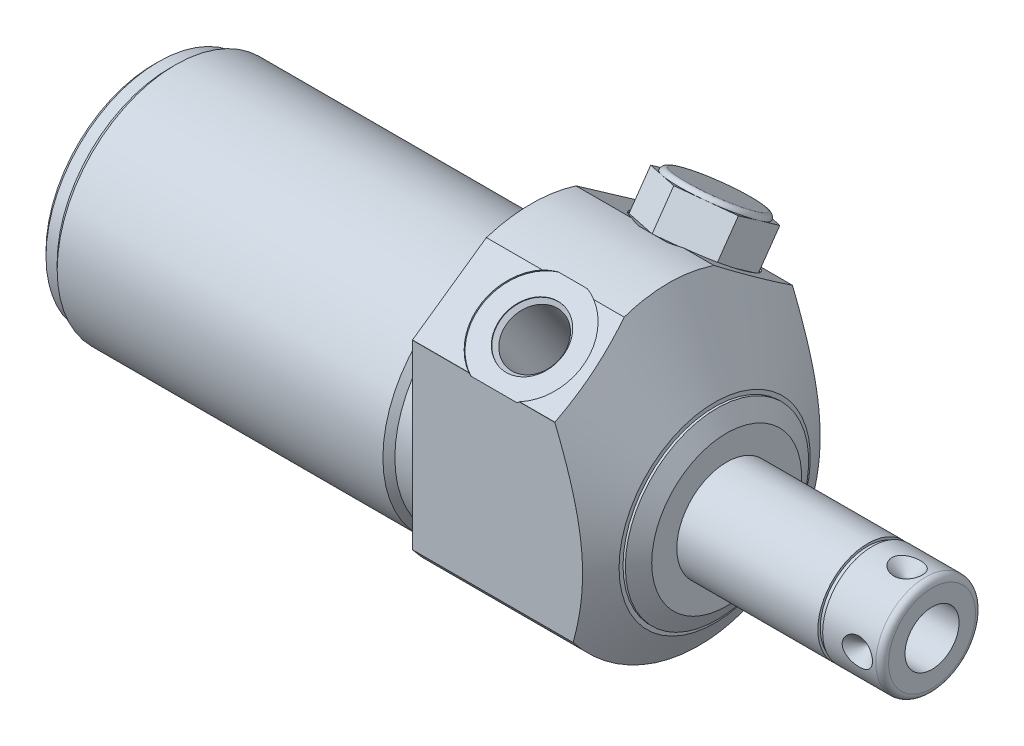
SolidWorks part; units mm, degrees
material "Alloy Steel"
ref_plane "Front Plane" through (0, 0, 0) normal (0, 0, 1) x (1, 0, 0)
ref_plane "Top Plane" through (0, 0, 0) normal (0, 1, 0) x (1, 0, 0)
ref_plane "Right Plane" through (0, 0, 0) normal (1, 0, 0) x (0, 0, -1)
sketch "Sketch1" plane through (0, 0, 0) normal (1, 0, 0) x (0, 0, -1)
  circle A0 centre (0, 0) radius 25.4
  dimension "D1" = 50.8
extrude "Extrude1" add sketch "Sketch1" along normal blind 31.1404 and the other way blind 60.1472
sketch "Sketch2" plane through (0, 0, 0) normal (1, 0, 0) x (0, 0, -1)
  line L0 (-14.6964, -4.191) -> (14.6964, -4.191) construction
  circle A0 centre (0, -4.191) radius 18.8595
  circle A1 centre (0, 0) radius 25.4 construction
  circle A2 centre (0, 0) radius 25.4
  dimension "D1" = 37.719
  dimension "D2" = 4.191
extrude "Cut-Extrude1" cut sketch "Sketch2" against normal up to next
sketch "Sketch4" plane through (31.1404, 0, 0) normal (-1, 0, 0) x (0, 0, 1)
  line L0 (18.923, -14.4553) -> (18.923, 14.4553)
  line L1 (18.9056, 14.4781) -> (7.1389, 22.7172)
  line L2 (-18.923, -14.4553) -> (-18.923, 14.4553)
  line L3 (-18.9056, 14.4781) -> (-7.1389, 22.7172)
  line L4 (0, -20.9029) -> (0, 19.86) construction
  circle A0 centre (0, 0) radius 25.4 construction
  circle A1 centre (0, 0) radius 25.4
  arc A2 (-18.923, -14.4553) -> (18.923, -14.4553) centre (0, 0) ccw
  arc A3 (7.1389, 22.7172) -> (-7.1389, 22.7172) centre (0, 0) ccw
  arc A4 (18.923, 14.4553) -> (18.9056, 14.4781) centre (0, 0) ccw
  arc A6 (-18.9056, 14.4781) -> (-18.923, 14.4553) centre (0, 0) ccw
  dimension "D4" = 23.8125
  dimension "D1" = 37.846
  dimension "D2" = 55
  dimension "D3" = 26.1366
extrude "Cut-Extrude3" cut sketch "Sketch4" along normal up to next
sketch "Sketch6" plane through (0, 0, 0) normal (0, 0, 1) x (1, 0, 0)
  line L0 (16.3822, 33.309) -> (29.2354, 11.0466)
  line L1 (1.9872, -4.191) -> (19.8625, -4.191) construction
  line L2 (-60.1472, -4.191) -> (0, -4.191) construction
  line L4 (31.1404, 7.747) -> (31.1404, 33.309)
  line L5 (31.1404, 33.309) -> (16.3822, 33.309)
  line L7 (29.2354, 11.0466) -> (29.2354, 10.414)
  line L8 (29.2354, 10.414) -> (29.6006, 10.414)
  line L9 (29.6006, 10.414) -> (31.1404, 7.747)
  line L11 (31.1404, -14.4553) -> (31.1404, 14.4553) construction
  dimension "D1" = 23.876
  dimension "D2" = 75
  dimension "D3" = 29.21
  dimension "D4" = 1.905
  dimension "D5" = 30
revolve "Cut-Revolve2" cut sketch "Sketch6" angle 360 about L1
ref_plane "Plane17" through (13.0048, 0, 0) normal (-1, 0, 0) x (0, 0, 1)
sketch "S2D0002" plane through (13.0048, 13.7124, 8.6091) normal (1, 0, 0) x (0, 0.4226, -0.9063)
  line L0 (3.0583, 6.9151) -> (6.2476, 7.4775)
  line L1 (3.0583, 6.9151) -> (3.0804, 6.7901)
  line L2 (3.0804, 6.7901) -> (2.5962, 6.0986)
  line L3 (2.5962, 6.0986) -> (4.8081, -6.446)
  line L4 (4.8081, -6.446) -> (0.4557, -7.2134)
  line L5 (0.4557, -7.2134) -> (-1.9261, 6.2942)
  line L6 (1.3861, -12.4899) -> (-0.9428, 0.7176) construction
  line L7 (6.2035, 7.7276) -> (6.2476, 7.4775)
  line L8 (5.1381, 7.5398) -> (-9.0082, 5.0454) construction
  line L9 (6.2035, 7.7276) -> (-1.9261, 6.2942)
  dimension "D1" = 16.51
  dimension "D2" = 0.254
  dimension "D3" = 0.127
  dimension "D4" = 10.033
  dimension "D5" = 45
  dimension "D6" = 8.8392
  dimension "D7" = 13.462
  dimension "D8" = 2.413
revolve "Cut-Revolve3" cut sketch "S2D0002" angle 360 about L6
mirror "Mirror1" about plane through (0, 0, 0) normal (0, 0, 1) of "Cut-Revolve3"
sketch "Sketch10" plane through (0, 0, 0) normal (0, 0, 1) x (1, 0, 0)
  line L0 (0, 14.6685) -> (0, 13.716)
  line L1 (0, 13.716) -> (-3.81, 13.716)
  line L2 (-3.81, 13.716) -> (-4.7625, 14.6685)
  line L3 (-5.094, -4.191) -> (0.2426, -4.191) construction
  line L4 (0, 14.6685) -> (-4.7625, 14.6685)
  line L5 (-60.1472, -4.191) -> (0, -4.191) construction
  line L6 (0, 14.6685) -> (-60.1472, 14.6685) construction
  line L7 (0, 14.4553) -> (0, -14.4553) construction
  dimension "D1" = 35.814
  dimension "D2" = 3.81
  dimension "D3" = 45
revolve "Cut-Revolve6" cut sketch "Sketch10" angle 360 about L3
sketch "Sketch12" plane through (0, 0, 0) normal (0, 0, 1) x (1, 0, 0)
  line L0 (-60.1472, 14.6685) -> (-60.1472, 13.716)
  line L1 (-60.1472, 13.716) -> (-57.6072, 13.716)
  line L2 (-57.6072, 13.716) -> (-56.6547, 14.6685)
  line L3 (-50.9283, -4.191) -> (-48.1063, -4.191) construction
  line L4 (-60.1472, 14.6685) -> (-56.6547, 14.6685)
  line L5 (-60.1472, -4.191) -> (-4.7625, -4.191) construction
  line L6 (-4.7625, 14.6685) -> (-60.1472, 14.6685) construction
  line L7 (-60.1472, 14.6685) -> (-60.1472, -23.0505) construction
  dimension "D1" = 35.814
  dimension "D2" = 2.54
  dimension "D3" = 45
revolve "Cut-Revolve8" cut sketch "Sketch12" angle 360 about L3
chamfer "Chamfer1" distance 0.762 angle 45 1 edges at (-60.1472, -4.191, 17.907)
sketch "Sketch13" plane through (0, 0, 0) normal (0, 0, 1) x (1, 0, 0)
  line L0 (31.1404, -4.191) -> (63.856, -4.191)
  line L1 (63.856, -4.191) -> (63.856, -11.1125)
  line L2 (62.84, -12.1285) -> (31.1404, -12.1285)
  line L3 (31.1404, -12.1285) -> (31.1404, -4.191)
  line L4 (4.7498, -4.191) -> (27.0459, -4.191) construction
  line L5 (-56.6547, -4.191) -> (-4.7625, -4.191) construction
  line L6 (31.1404, -16.129) -> (31.1404, 7.747) construction
  line L7 (0, 14.4553) -> (0, -14.4553) construction
  arc A0 (62.84, -12.1285) -> (63.856, -11.1125) centre (62.84, -11.1125) ccw
  dimension "D2" = 1.016
  dimension "D1" = 63.856
  dimension "D3" = 15.875
revolve "Revolve1" add sketch "Sketch13" angle 360 about L4
sketch "S2D0001" plane through (0, 0, 0) normal (0, 0, 1) x (1, 0, 0)
  line L0 (63.856, 0.1143) -> (48.616, 0.1143)
  line L1 (48.616, 0.1143) -> (46.0291, -4.191)
  line L2 (63.856, 0.1143) -> (63.856, -4.191)
  line L3 (63.856, -4.191) -> (46.0291, -4.191)
  line L4 (-2.8067, -4.191) -> (-15.8378, -4.191) construction
  line L5 (62.84, -4.191) -> (31.1404, -4.191) construction
  line L6 (63.856, -11.1125) -> (63.856, 2.7305) construction
  dimension "D1" = 8.6106
  dimension "D2" = 15.24
  dimension "D3" = 59
revolve "Cut-Revolve9" cut sketch "S2D0001" angle 360 about L4
ref_plane "Plane18" through (0, 0, 0) normal (0, 0, 1) x (-1, 0, 0)
sketch "Sketch15" plane through (0, 18.3896, -12.8765) normal (0, 0.8192, -0.5736) x (-1, 0, 0)
  line L1 (-13.0048, 8.0747) -> (-19.9898, 4.0419)
  line L2 (-19.9898, 4.0419) -> (-19.9898, -4.0237)
  line L3 (-19.9898, -4.0237) -> (-13.0048, -8.0564)
  line L4 (-13.0048, -8.0564) -> (-6.0198, -4.0237)
  line L5 (-6.0198, -4.0237) -> (-6.0198, 4.0419)
  line L6 (-6.0198, 4.0419) -> (-13.0048, 8.0747)
  circle A1 centre (-13.0048, 0.0091) radius 6.985 construction
  dimension "D2" = 13.97
extrude "Extrude2" add sketch "Sketch15" along normal blind 6.78
sketch "Sketch16" plane through (0, -7.1545, 0) normal (0, 0, -1) x (1, 0, 0)
  line L0 (59.8936, -10.901) -> (57.4806, -10.901)
  line L1 (57.4806, -10.901) -> (59.8936, -8.488)
  line L2 (59.8936, -10.901) -> (59.8936, -8.488)
  line L3 (59.8936, -3.4788) -> (59.8936, 0.0794) construction
  line L4 (63.856, -9.885) -> (63.856, 3.958) construction
  line L5 (31.1404, -10.901) -> (62.84, -10.901) construction
  dimension "D1" = 3.9624
  dimension "D2" = 4.826
  dimension "D3" = 45
revolve "Cut-Revolve10" cut sketch "Sketch16" angle 360 about L3
sketch "Sketch21" plane through (0, 0, 0) normal (0, 0, 1) x (1, 0, 0)
  line L1 (53.6066, 3.7465) -> (54.3686, 3.7465)
  line L2 (53.6066, 3.7465) -> (53.6066, 3.3655)
  line L3 (53.6066, 3.3655) -> (54.3686, 3.3655)
  line L4 (54.3686, 3.7465) -> (54.3686, 3.3655)
  line L5 (53.9876, -0.7782) -> (53.9876, 2.3032) construction
  line L7 (23.8735, -4.191) -> (50.6625, -4.191) construction
  line L10 (63.856, -11.1125) -> (63.856, 2.7305) construction
  line L11 (67.3347, -4.191) -> (53.8506, -4.191) construction
  dimension "D1" = 0.381
  dimension "D2" = 0.762
  dimension "D3" = 9.4874
  dimension "D4" = 7.9375
revolve "Cut-Revolve11" cut sketch "Sketch21" angle 360 about L7
ref_plane "Plane19" through (0, 0.0052, 0.0075) normal (0, 0.5736, 0.8192) x (1, 0, 0)
sketch "Sketch22" plane through (0, 0.0052, 0.0075) normal (0, 0.5736, 0.8192) x (1, 0, 0)
  line L5 (19.9898, 28.4675) -> (29.9276, 28.4675)
  line L6 (19.2278, 29.2295) -> (19.2278, 42.2087)
  line L7 (19.2278, 42.2087) -> (29.9276, 42.2087)
  line L8 (29.9276, 28.4675) -> (29.9276, 42.2087)
  arc A0 (19.2278, 29.2295) -> (19.9898, 28.4675) centre (19.2278, 28.4675) cw
revolve "Cut-Revolve12" cut sketch "Sketch22" angle 360 about axis through (13.0048, 2.9785, -2.0744) along (0, -0.8192, 0.5736)
pattern_circular "CirPattern1" count 4 over 360 about axis through (4.7498, -4.191, 0) along (-1, 0, 0) of "Cut-Revolve10"
